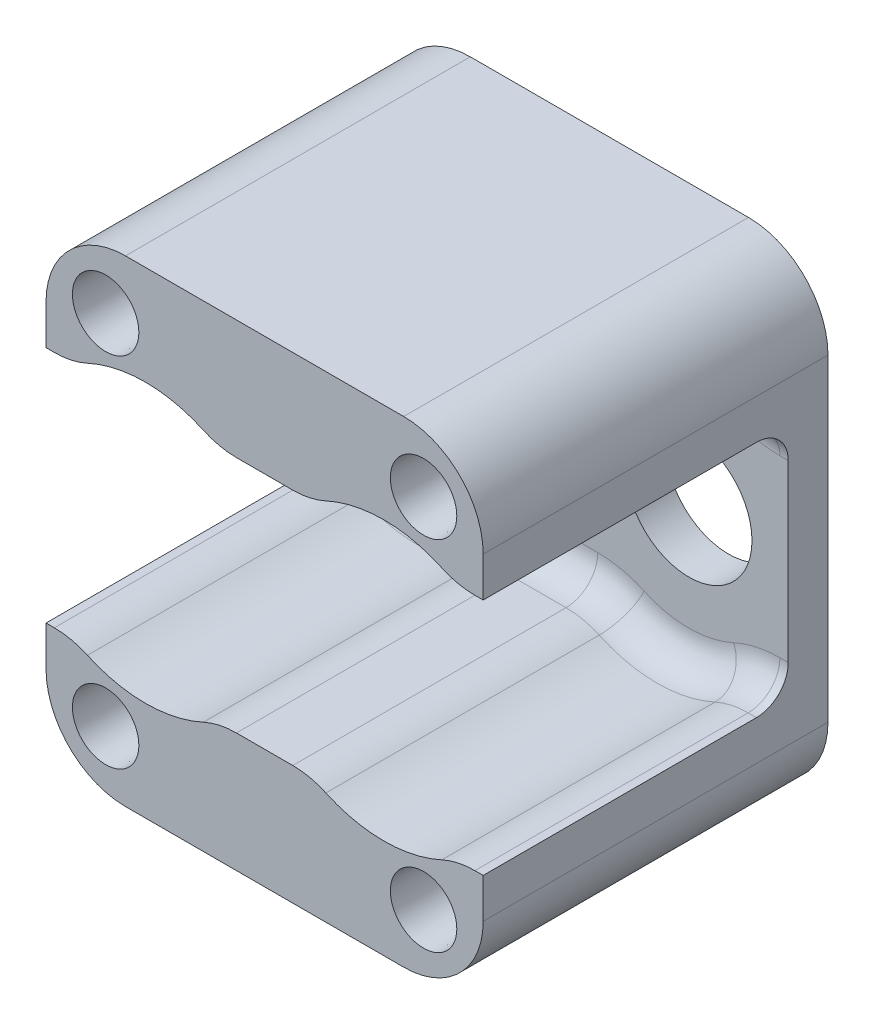
SolidWorks part; units mm, degrees
material "PET"
ref_plane "Front Plane" through (0, 0, 0) normal (0, 0, 1) x (1, 0, 0)
ref_plane "Top Plane" through (0, 0, 0) normal (0, 1, 0) x (1, 0, 0)
ref_plane "Right Plane" through (0, 0, 0) normal (1, 0, 0) x (0, 0, -1)
sketch "Sketch1" plane through (0, 0, 0) normal (0, 0, 1) x (1, 0, 0)
  line L0 (-19.05, 0) -> (0, 0) construction
  line L2 (7.9375, -19.05) -> (-26.9875, -19.05)
  line L3 (7.9375, -19.05) -> (7.9375, 19.05)
  line L4 (7.9375, 19.05) -> (-26.9875, 19.05)
  line L5 (-26.9875, -19.05) -> (-26.9875, 19.05)
  line L6 (7.9375, -19.05) -> (-26.9875, 19.05) construction
  line L7 (7.9375, 19.05) -> (-26.9875, -19.05) construction
  point P4 (-9.525, 0)
  dimension "D1" = 34.925
  dimension "D2" = 38.1
extrude "Boss-Extrude1" add sketch "Sketch1" along normal blind 3.175
sketch "Sketch2" plane through (0, 0, 3.175) normal (0, 0, 1) x (1, 0, 0)
  line L0 (7.9375, -19.05) -> (7.9375, 19.05) construction
  line L1 (-26.9875, 19.05) -> (7.9375, 19.05)
  line L2 (-26.9875, 19.05) -> (-26.9875, 9.525)
  line L3 (-26.9875, 9.525) -> (7.9375, 9.525)
  line L4 (7.9375, 19.05) -> (7.9375, 9.525)
  dimension "D1" = 9.525
extrude "Boss-Extrude2" add sketch "Sketch2" along normal up to surface (24.3713 mm away)
sketch "Sketch3" plane through (0, 0, 19.6088) normal (0, 0, 1) x (1, 0, 0)
  circle A0 centre (-19.05, 0) radius 11.1125
  circle A1 centre (0, 0) radius 11.1125
  dimension "D1" = 22.225
extrude "Cut-Extrude1" cut sketch "Sketch3" against normal up to surface (16.4338 mm away) and the other way through all contours A1 A0 | A0 A1 | A0 A1 up to face at (-13.8906, -4.7625, 3.175)
mirror "Mirror1" about plane through (0, 0, 0) normal (0, 1, 0) of "Cut-Extrude1", "Boss-Extrude2"
fillet "Fillet1" radius 6.35 12 edges at (7.9375, 19.05, 13.7732) (-26.9875, 19.05, 13.7732) (5.7238, 9.525, 15.3607) (-5.7238, 9.525, 15.3607) (-13.3262, 9.525, 15.3607) (-24.7738, 9.525, 15.3607) (7.9375, -19.05, 13.7732) (-26.9875, -19.05, 13.7732) (5.7238, -9.525, 15.3607) (-5.7238, -9.525, 15.3607) (-13.3262, -9.525, 15.3607) (-24.7738, -9.525, 15.3607)
fillet "Fillet2" radius 2.54 18 edges at (5.921, 9.671, 3.175) (0, 11.1125, 3.175) (-5.921, 9.671, 3.175) (-13.129, 9.671, 3.175) (-19.05, 11.1125, 3.175) (-24.971, 9.671, 3.175) (7.6062, -9.525, 3.175) (5.921, -9.671, 3.175) (0, -11.1125, 3.175) (-5.921, -9.671, 3.175) (-9.525, -9.525, 3.175) (-13.129, -9.671, 3.175) (-19.05, -11.1125, 3.175) (-24.971, -9.671, 3.175) (-26.6562, -9.525, 3.175)
sketch "Sketch4" plane through (0, 0, 3.175) normal (0, 0, 1) x (1, 0, 0)
  line L0 (-10.9857, 8.0643) -> (-27.1143, -8.0643) construction
  line L2 (-26.2611, -8.9174) -> (-27.9674, -7.2111) construction
  circle A0 centre (-19.05, 0) radius 4.9022
  point P8 (-19.05, 0)
  point P10 (-19.05, 0)
  dimension "D1" = 9.8044
extrude "Cut-Extrude2" cut sketch "Sketch4" against normal through all
hole_wizard "3/8 Clearance Hole1" positions "Sketch6" profile "Sketch5" hole size "3/8" standard "ANSI Inch" end condition through all
sketch "Sketch6" plane through (0, 0, 3.175) normal (0, 0, 1) x (1, 0, 0)
  point P0 (0, 0)
sketch "Sketch5" plane through (0, 0, 3.175) normal (1, 0, 0) x (0, -1, 0)
  line L0 (0, 0) -> (0, 3.175)
  line L1 (0, 3.175) -> (5.0419, 3.175)
  line L2 (5.0419, 3.175) -> (5.0419, 0)
  line L5 (5.0419, 0) -> (0, 0)
  line L11 (0, -6.35) -> (0, 107.95) construction
  dimension "Thru Hole Dia." = 10.0838
  dimension "Thru Hole Depth" = 3.175
hole_wizard "#6 Clearance Hole1" positions "Sketch8" profile "Sketch7" hole size "#6" standard "ANSI Inch" end condition through all
sketch "Sketch8" plane through (0, 0, 0) normal (0, 0, -1) x (-1, 0, 0)
  line L0 (-7.9375, -12.7) -> (-7.9375, 12.7) construction
  line L1 (-1.5875, 19.05) -> (20.6375, 19.05) construction
  line L2 (9.525, 19.05) -> (9.525, 0) construction
  line L3 (9.525, 0) -> (26.9875, 0) construction
  line L4 (26.9875, 12.7) -> (26.9875, -12.7) construction
  point P0 (-3.175, 14.2875)
  point P21 (22.225, 14.2875)
  point P23 (22.225, -14.2875)
  point P24 (-3.175, -14.2875)
  dimension "D1" = 4.7625
  dimension "D2" = 4.7625
sketch "Sketch7" plane through (3.175, 14.2875, 0) normal (1, 0, 0) x (0, 1, 0)
  line L0 (0, 0) -> (0, 27.5463)
  line L1 (0, 27.5463) -> (2.1526, 27.5463)
  line L2 (2.1526, 27.5463) -> (2.1526, 0)
  line L5 (2.1526, 0) -> (0, 0)
  line L11 (0, -6.35) -> (0, 107.95) construction
  dimension "Thru Hole Dia." = 4.3053
  dimension "Thru Hole Depth" = 27.5463
hole_wizard "Hole1" positions "Sketch10" profile "Sketch9" legacy
sketch "Sketch10" plane through (0, 0, 27.5463) normal (0, 0, 1) x (1, 0, 0)
  point P0 (-22.225, 14.2875)
  point P3 (3.175, 14.2875)
  point P6 (-22.225, -14.2875)
  point P9 (3.175, -14.2875)
sketch "Sketch9" plane through (-22.225, 14.2875, 27.5463) normal (1, 0, 0) x (0, -1, 0)
  line L0 (0, 0) -> (0, 3.81)
  line L1 (0, 3.81) -> (2.5273, 3.81)
  line L2 (2.5273, 3.81) -> (2.6543, 0)
  line L3 (2.6543, 0) -> (0, 0)
  line L4 (0, 110) -> (0, -10) construction
  dimension "Minor Diameter" = 5.0546
  dimension "Depth" = 3.81
  dimension "Major Diameter" = 5.3086
sketch "Sketch11" plane through (0, 0, 0) normal (0, 0, -1) x (-1, 0, 0)
  circle A0 centre (23.8252, -8.2709) radius 1.5875
  dimension "D1" = 3.175
extrude "Cut-Extrude3" cut sketch "Sketch11" against normal up to next
hole_wizard "Hole2" positions "Sketch13" profile "Sketch12" legacy
sketch "Sketch13" plane through (0, 0, 0) normal (0, 0, -1) x (-1, 0, 0)
  point P0 (22.225, 14.2875)
sketch "Sketch12" plane through (-22.225, 14.2875, 0) normal (1, 0, 0) x (0, 1, 0)
  line L0 (0, 0) -> (0, 3.81)
  line L1 (0, 3.81) -> (2.5273, 3.81)
  line L2 (2.5273, 3.81) -> (2.6543, 0)
  line L3 (2.6543, 0) -> (0, 0)
  line L4 (0, 110) -> (0, -10) construction
  dimension "Minor Diameter" = 5.0546
  dimension "Depth" = 3.81
  dimension "Major Diameter" = 5.3086
